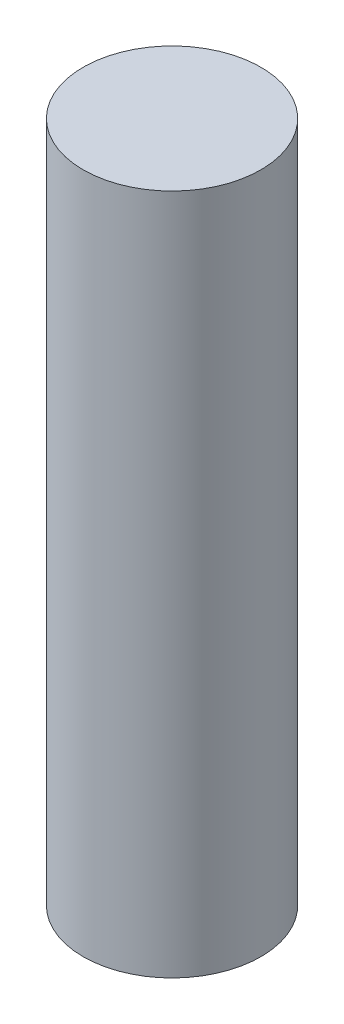
SolidWorks part; units mm, degrees
ref_plane "Front Plane" through (0, 0, 0) normal (0, 0, 1) x (1, 0, 0)
ref_plane "Top Plane" through (0, 0, 0) normal (0, 1, 0) x (1, 0, 0)
ref_plane "Right Plane" through (0, 0, 0) normal (1, 0, 0) x (0, 0, -1)
sketch "Sketch2" plane through (0, 0, 0) normal (0, 1, 0) x (1, 0, 0)
  circle A0 centre (0, 0) radius 3.9751
  dimension "D1" = 7.9502
extrude "Boss-Extrude1" add sketch "Sketch2" along normal blind 30.48
sketch "Sketch3" plane through (0, 0, 0) normal (0, -1, 0) x (1, 0, 0)
  line L0 (6.9215, -12.319) -> (1.524, -12.319)
  line L1 (-12.319, 1.5748) -> (12.319, 1.5748)
  line L2 (-12.319, 1.5748) -> (-12.319, -1.5748) construction
  line L3 (-12.319, -1.5748) -> (12.319, -1.5748)
  line L4 (12.319, 1.5748) -> (12.319, -1.5748) construction
  line L5 (-12.319, 1.5748) -> (12.319, -1.5748) construction
  line L6 (-12.319, -1.5748) -> (12.319, 1.5748) construction
  line L7 (-1.524, 12.319) -> (1.524, 12.319) construction
  line L8 (-1.524, 12.319) -> (-1.524, -12.319)
  line L9 (-1.524, -12.319) -> (1.524, -12.319) construction
  line L10 (1.524, 12.319) -> (1.524, -12.319)
  line L11 (-1.524, 12.319) -> (1.524, -12.319) construction
  line L12 (-1.524, -12.319) -> (1.524, 12.319) construction
  line L13 (-12.319, -6.9215) -> (-6.9215, -12.319)
  line L14 (-1.524, -12.319) -> (-6.9215, -12.319)
  line L15 (6.9215, -12.319) -> (12.319, -6.9215)
  line L16 (12.319, -6.9215) -> (12.319, -1.5748)
  line L17 (12.319, 6.9215) -> (6.9215, 12.319)
  line L18 (-12.319, -6.9215) -> (-12.319, -1.5748)
  line L19 (-6.9215, 12.319) -> (-12.319, 6.9215)
  line L20 (-6.9215, -12.319) -> (-12.319, -12.319) construction
  line L21 (-12.319, -12.319) -> (-12.319, -6.9215) construction
  line L22 (-12.319, 6.9215) -> (-12.319, 12.319) construction
  line L23 (-12.319, 12.319) -> (-6.9215, 12.319) construction
  line L24 (6.9215, -12.319) -> (12.319, -12.319) construction
  line L25 (12.319, -12.319) -> (12.319, -6.9215) construction
  line L26 (12.319, 6.9215) -> (12.319, 12.319) construction
  line L27 (12.319, 12.319) -> (6.9215, 12.319) construction
  line L28 (9.6202, -9.6202) -> (-9.6202, 9.6202) construction
  line L29 (9.6202, 9.6202) -> (-9.6202, -9.6202) construction
  line L30 (7.9736, -14.859) -> (-7.9736, -14.859)
  line L31 (-7.9736, -14.859) -> (-14.859, -7.9736)
  line L32 (-14.859, -7.9736) -> (-14.859, 7.9736)
  line L33 (-14.859, 7.9736) -> (-7.9736, 14.859)
  line L34 (-7.9736, 14.859) -> (7.9736, 14.859)
  line L35 (7.9736, 14.859) -> (14.859, 7.9736)
  line L37 (14.859, -7.9736) -> (7.9736, -14.859)
  line L38 (7.9736, -14.859) -> (6.9215, -12.319) construction
  line L39 (12.319, 1.5748) -> (12.319, 6.9215)
  line L40 (14.859, -7.9736) -> (14.859, 7.9736)
  line L41 (-12.319, 1.5748) -> (-12.319, 6.9215)
  line L42 (-6.9215, 12.319) -> (-1.524, 12.319)
  line L43 (1.524, 12.319) -> (6.9215, 12.319)
  point P0 (0, 0)
  point P6 (0, 0)
  point P30 (0, 0)
  circle M9 centre (0, 0) radius 3.9751
  dimension "D4" = 13.843
  dimension "D1" = 3.1496
  dimension "D2" = 3.048
  dimension "D3" = 24.638
  dimension "D5" = 2.54
  dimension "D6" = 2.54
  dimension "D7" = 2.54
  dimension "D8" = 2.54
  dimension "D9" = 2.54
  dimension "D10" = 2.54
  dimension "D11" = 2.54
  dimension "D12" = 2.54
extrude "Adapter Holders" [suppressed] add sketch "Sketch3" against normal blind 4.318 contours L37 L40 L35 L34 L33 L32 L31 L30 L10 L43 L17 L39 L1 L3 L16 L15 L0 L8 L14 L13 L18 L41 L19 L42 M9
fillet "Fillet1" [suppressed] radius 3.556
sketch "Sketch4" plane through (0, 30.48, 0) normal (0, 1, 0) x (1, 0, 0)
  circle A0 centre (0, 0) radius 2.032
  dimension "D1" = 4.064
extrude "Magnet Hole" [suppressed] cut sketch "Sketch4" against normal blind 2.0066
